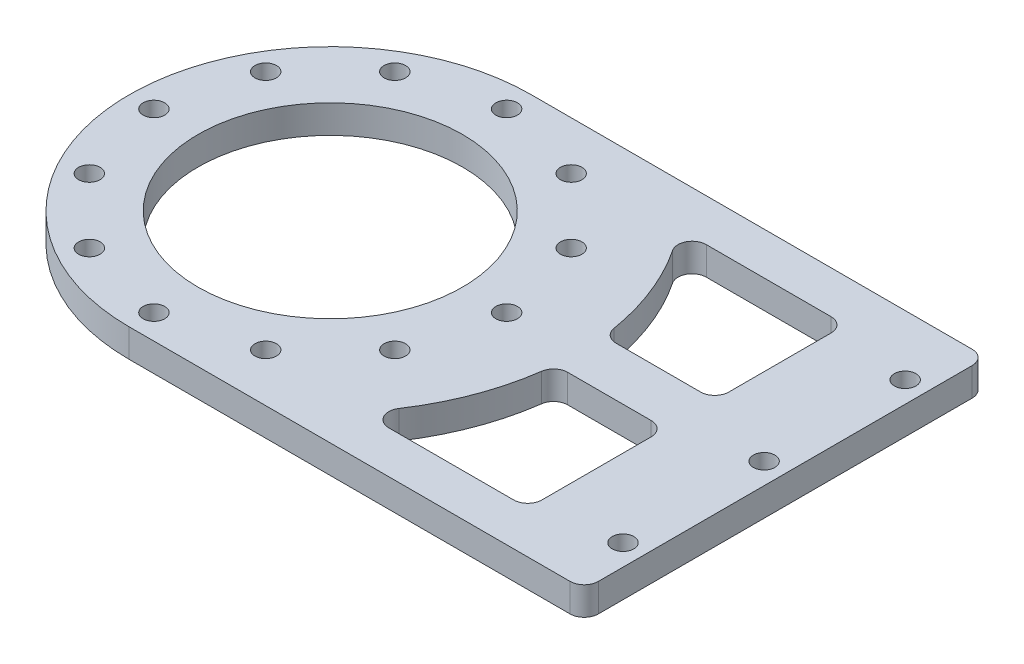
SolidWorks part; units mm, degrees
material "Thornel Mat VMA"
ref_plane "前视基准面" through (0, 0, 0) normal (0, 0, 1) x (1, 0, 0)
ref_plane "上视基准面" through (0, 0, 0) normal (0, 1, 0) x (1, 0, 0)
ref_plane "右视基准面" through (0, 0, 0) normal (1, 0, 0) x (0, 0, -1)
other "Configuration Table"
sketch "草图1" plane through (0, 0, 0) normal (0, 1, 0) x (1, 0, 0)
  line L1 (-32.25, -28.5) -> (32.25, -28.5)
  line L2 (-32.25, -28.5) -> (-32.25, 28.5)
  line L3 (-32.25, 28.5) -> (32.25, 28.5)
  line L4 (32.25, -28.5) -> (32.25, 28.5)
  line L5 (-32.25, -28.5) -> (32.25, 28.5) construction
  line L6 (-32.25, 28.5) -> (32.25, -28.5) construction
  circle A0 centre (-32.25, 0) radius 28.5
  point P0 (0, 0)
  dimension "D1" = 57
  dimension "D2" = 64.5
extrude "凸台-拉伸1" add sketch "草图1" along normal blind 4 contours L2 A0 | L2 A0 | A0 L1 L4 L3
sketch "草图2" plane through (0, 4, 0) normal (0, 1, 0) x (1, 0, 0)
  circle A0 centre (-32.25, 0) radius 13.5 construction
  circle A1 centre (-45.75, 0) radius 1.525
  circle A2 centre (-39, 11.6913) radius 1.525
  circle A3 centre (-25.5, 11.6913) radius 1.525
  circle A4 centre (-18.75, 0) radius 1.525
  circle A5 centre (-25.5, -11.6913) radius 1.525
  circle A6 centre (-39, -11.6913) radius 1.525
  point P17 (-32.25, 0)
  dimension "D1" = 27
  dimension "D2" = 3.05
  dimension "D3" = 6
extrude "切除-拉伸1" cut sketch "草图2" against normal through all
sketch "草图4" plane through (0, 4, 0) normal (0, 1, 0) x (1, 0, 0)
  circle A0 centre (-32.25, 0) radius 10
  dimension "D1" = 20
extrude "切除-拉伸2" cut sketch "草图4" against normal through all
sketch "草图5" plane through (0, 4, 0) normal (0, 1, 0) x (1, 0, 0)
  line L0 (-43.25, 19.0526) -> (-32.25, 0) construction
  line L1 (-32.25, 22) -> (-32.25, 0) construction
  arc A0 (-43.25, 19.0526) -> (-21.25, 19.0526) centre (-32.25, 0) cw construction
  arc A1 (-19.25, 22.5167) -> (-45.25, 22.5167) centre (-32.25, 0) ccw
  arc A2 (-23.25, 15.5885) -> (-41.25, 15.5885) centre (-32.25, 0) ccw
  arc A3 (-23.25, 15.5885) -> (-19.25, 22.5167) centre (-21.25, 19.0526) ccw
  arc A4 (-45.25, 22.5167) -> (-41.25, 15.5885) centre (-43.25, 19.0526) ccw
  arc A6 (-23.25, -15.5885) -> (-14.25, 0) centre (-32.25, 0) ccw
  arc A7 (-23.25, -15.5885) -> (-19.25, -22.5167) centre (-21.25, -19.0526) ccw
  arc A8 (-6.25, 0) -> (-14.25, 0) centre (-10.25, 0) ccw
  arc A9 (-19.25, -22.5167) -> (-6.25, 0) centre (-32.25, 0) ccw
  arc A10 (-10.25, 0) -> (-21.25, -19.0526) centre (-32.25, 0) cw construction
  arc A11 (-50.25, 0) -> (-41.25, -15.5885) centre (-32.25, 0) ccw
  arc A12 (-50.25, 0) -> (-58.25, 0) centre (-54.25, 0) ccw
  arc A13 (-45.25, -22.5167) -> (-41.25, -15.5885) centre (-43.25, -19.0526) ccw
  arc A14 (-58.25, 0) -> (-45.25, -22.5167) centre (-32.25, 0) ccw
  arc A15 (-43.25, -19.0526) -> (-54.25, 0) centre (-32.25, 0) cw construction
  point P4 (-32.25, 22)
  point P11 (0, 0)
  point P17 (-13.1974, -11)
  point P24 (-51.3026, -11)
  point P29 (-32.25, 0)
  dimension "D1" = 22
  dimension "D2" = 4
  dimension "D3" = 30
  dimension "D4" = 3
sketch "草图7" plane through (0, 4, 0) normal (0, 1, 0) x (1, 0, 0)
  circle A0 centre (-32.25, 0) radius 18.75
  dimension "D1" = 37.5
extrude "切除-拉伸4" cut sketch "草图7" against normal through all
sketch "草图8" plane through (0, 4, 0) normal (0, 1, 0) x (1, 0, 0)
  circle A0 centre (-32.25, 0) radius 25 construction
  circle A1 centre (-32.25, 25) radius 1.525
  circle A2 centre (-19.75, 21.6506) radius 1.525
  circle A3 centre (-10.5994, 12.5) radius 1.525
  circle A4 centre (-7.25, 0) radius 1.525
  circle A5 centre (-10.5994, -12.5) radius 1.525
  circle A6 centre (-19.75, -21.6506) radius 1.525
  circle A7 centre (-32.25, -25) radius 1.525
  circle A8 centre (-44.75, -21.6506) radius 1.525
  circle A9 centre (-53.9006, -12.5) radius 1.525
  circle A10 centre (-57.25, 0) radius 1.525
  circle A11 centre (-53.9006, 12.5) radius 1.525
  circle A12 centre (-44.75, 21.6506) radius 1.525
  point P30 (-32.25, 0)
  dimension "D1" = 50
  dimension "D2" = 3.05
  dimension "D3" = 12
extrude "切除-拉伸5" cut sketch "草图8" against normal through all
sketch "草图9" plane through (0, 4, 0) normal (0, 1, 0) x (1, 0, 0)
  line L0 (29.25, 17.0122) -> (29.25, 50017.0122) construction
  line L1 (32.25, -28.5) -> (32.25, 28.5) construction
  line L2 (0, 0) -> (29.25, 0) construction
  circle A0 centre (29.25, 0) radius 1.525
  circle A1 centre (29.25, 20) radius 1.525
  circle A2 centre (29.25, -20) radius 1.525
  dimension "D2" = 3.05
  dimension "D3" = 3.05
  dimension "D1" = 3
  dimension "D4" = 20
extrude "切除-拉伸6" cut sketch "草图9" against normal through all
fillet "圆角1" radius 2 2 edges at (32.25, 2, -28.5) (32.25, 2, 28.5)
sketch "草图18" plane through (0, 4, 0) normal (0, 1, 0) x (1, 0, 0)
  line L0 (32.25, -26.5) -> (32.25, 26.5) construction
  line L1 (18.25, -22.5) -> (-22.7517, -22.5)
  line L2 (18.25, -22.5) -> (18.25, 22.5)
  line L3 (18.25, 22.5) -> (-22.7517, 22.5)
  line L4 (-22.7517, -22.5) -> (-22.7517, 22.5)
  line L5 (18.25, -22.5) -> (-22.7517, 22.5) construction
  line L6 (18.25, 22.5) -> (-22.7517, -22.5) construction
  line L7 (-32.25, 28.5) -> (30.25, 28.5) construction
  line L8 (-22.7517, 0) -> (18.25, 0) construction
  line L9 (-22.7517, -3) -> (18.25, -3)
  line L10 (-22.7517, 4) -> (18.25, 4)
  circle A1 centre (-32.25, 0) radius 35
  point P3 (-2.2509, 0)
  point P22 (11.5291, 22.5)
  dimension "D1" = 70
  dimension "D2" = 14
  dimension "D3" = 41.0017
  dimension "D4" = 6
  dimension "D5" = 3
  dimension "D6" = 4
extrude "切除-拉伸8" cut sketch "草图18" against normal through all contours A1 L10 L2 L3 | A1 L1 L2 L9
fillet "圆角2" radius 2 8 edges at (18.25, 2, -22.5) (18.25, 2, -4) (2.5207, 2, -4) (2.6212, 2, 3) (18.25, 2, 3) (18.25, 2, 22.5) (-5.4405, 2, 22.5) (-5.4405, 2, -22.5)
